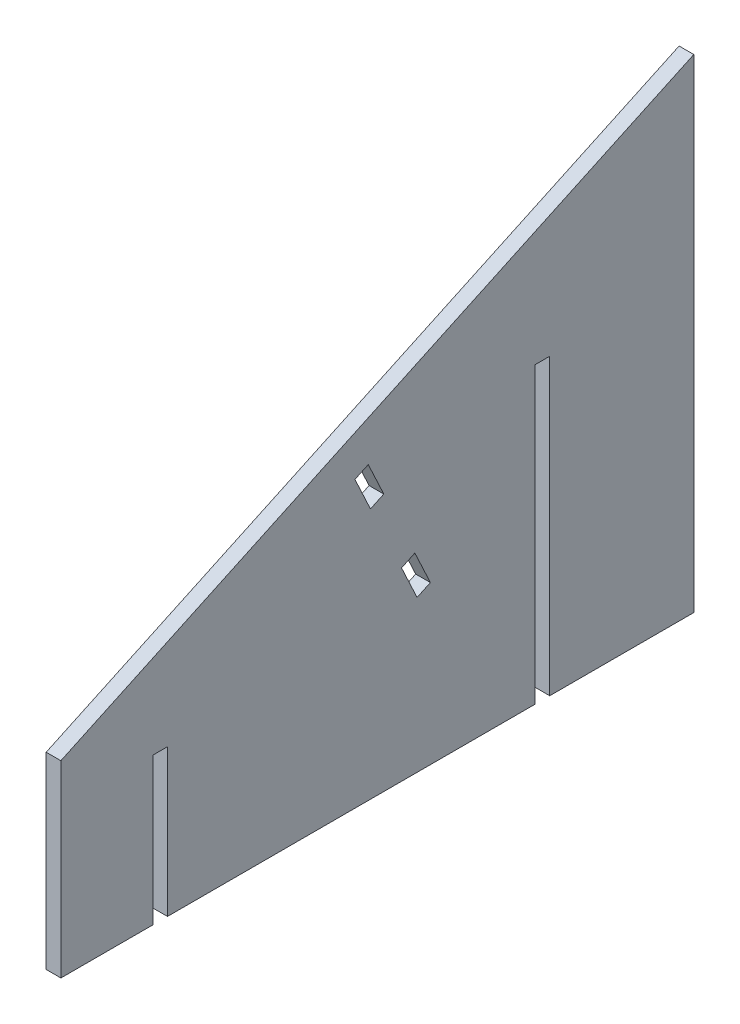
SolidWorks part; units mm, degrees
ref_plane "Front Plane" through (0, 0, 0) normal (0, 0, 1) x (1, 0, 0)
ref_plane "Top Plane" through (0, 0, 0) normal (0, 1, 0) x (1, 0, 0)
ref_plane "Right Plane" through (0, 0, 0) normal (1, 0, 0) x (0, 0, -1)
sketch "Sketch1" plane through (0, 0, 0) normal (1, 0, 0) x (0, 0, -1)
  line L0 (0, 0) -> (218.6921, 101.9778)
  line L1 (218.6921, 101.9778) -> (218.6921, -65.024)
  line L4 (0, 0) -> (0, -65.024)
  line L5 (0, -65.024) -> (218.6921, -65.024)
  point P6 (218.6921, -65.024)
  point P7 (218.6921, -29.806)
  dimension "D1" = 25
  dimension "D2" = 65.024
  dimension "D3" = 241.3
extrude "Boss-Extrude1" add sketch "Sketch1" along normal blind 5.08
sketch "Sketch2" plane through (5.08, 0, 0) normal (1, 0, 0) x (0, 0, -1)
  line L0 (101.6, 33.364) -> (106.204, 35.5109)
  line L1 (101.6, 33.364) -> (106.9673, 21.8538)
  line L2 (106.204, 35.5109) -> (111.5713, 24.0008)
  line L3 (106.9673, 21.8538) -> (111.5713, 24.0008)
  line L4 (218.6921, 101.9778) -> (0, 0) construction
  dimension "D1" = 12.7
  dimension "D2" = 5.08
  dimension "D3" = 12.7
  dimension "D4" = 101.6
extrude "Cut-Extrude1" cut sketch "Sketch2" against normal through all
pattern_linear "LPattern1" count 2 spacing 38.1 along (0, -0.9063, -0.4226) of "Cut-Extrude1"
sketch "Sketch3" plane through (5.08, 0, 0) normal (1, 0, 0) x (0, 0, -1)
  line L0 (0, -65.024) -> (218.6921, -65.024) construction
  line L1 (31.75, -65.024) -> (36.83, -65.024)
  line L2 (31.75, -65.024) -> (31.75, -14.224)
  line L3 (31.75, -14.224) -> (36.83, -14.224)
  line L4 (36.83, -65.024) -> (36.83, -14.224)
  line L5 (0, 0) -> (0, -65.024) construction
  line L6 (163.83, -65.024) -> (168.91, -65.024)
  line L7 (163.83, -65.024) -> (163.83, 36.576)
  line L8 (163.83, 36.576) -> (168.91, 36.576)
  line L9 (168.91, -65.024) -> (168.91, 36.576)
  dimension "D1" = 50.8
  dimension "D2" = 5.08
  dimension "D3" = 101.6
  dimension "D4" = 5.08
  dimension "D5" = 31.75
  dimension "D6" = 127
extrude "Cut-Extrude2" cut sketch "Sketch3" against normal through all
